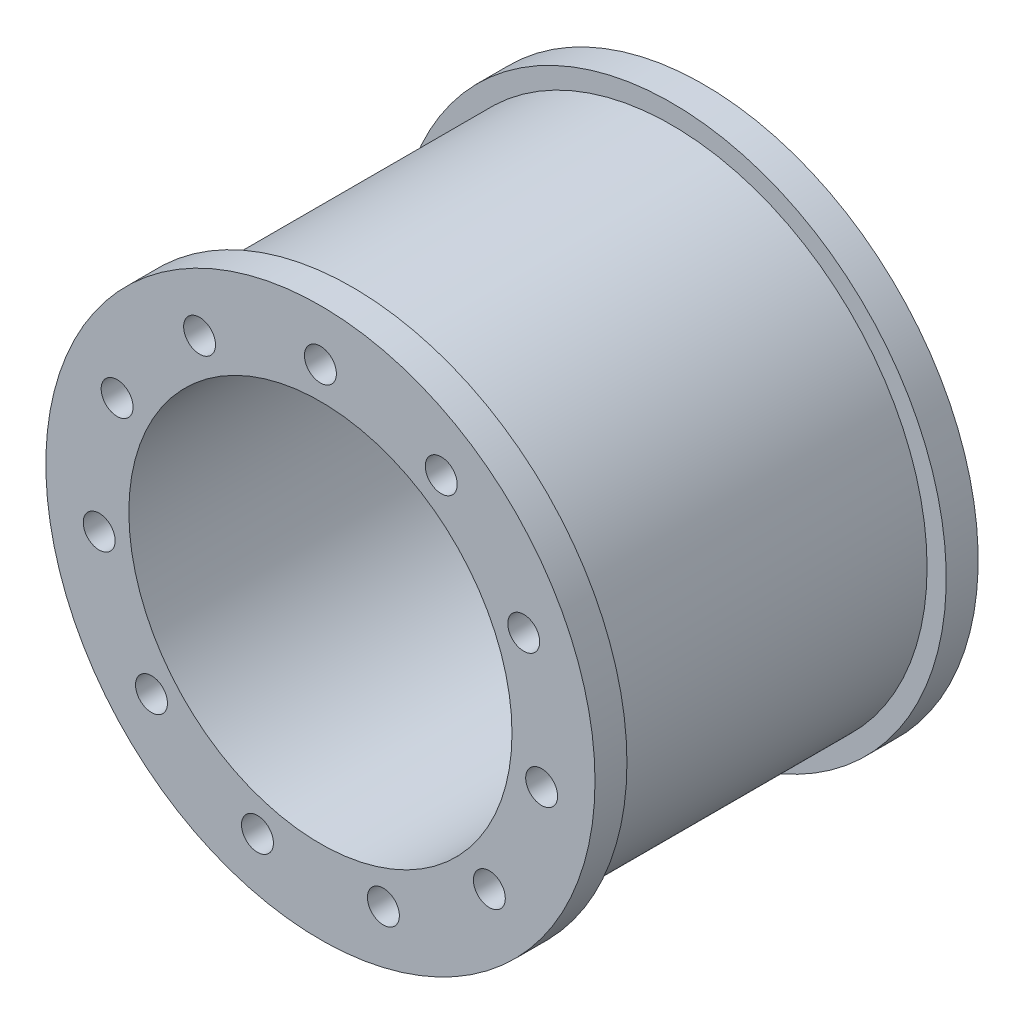
SolidWorks part; units mm, degrees
material "PET"
ref_plane "Front Plane" through (0, 0, 0) normal (0, 0, 1) x (1, 0, 0)
ref_plane "Top Plane" through (0, 0, 0) normal (0, 1, 0) x (1, 0, 0)
ref_plane "Right Plane" through (0, 0, 0) normal (1, 0, 0) x (0, 0, -1)
sketch "Sketch1" plane through (0, 0, 0) normal (0, 0, 1) x (1, 0, 0)
  circle A0 centre (0, 0) radius 40
  circle A1 centre (0, 0) radius 30
  circle A2 centre (0, 0) radius 35 construction
  circle A3 centre (0, 35) radius 2.5
  circle A4 centre (18.9224, 29.4439) radius 2.5
  circle A5 centre (31.8371, 14.5395) radius 2.5
  circle A6 centre (34.6438, -4.981) radius 2.5
  circle A7 centre (26.4512, -22.9201) radius 2.5
  circle A8 centre (9.8606, -33.5823) radius 2.5
  circle A9 centre (-9.8606, -33.5823) radius 2.5
  circle A10 centre (-26.4512, -22.9201) radius 2.5
  circle A11 centre (-34.6438, -4.981) radius 2.5
  circle A12 centre (-31.8371, 14.5395) radius 2.5
  circle A13 centre (-18.9224, 29.4439) radius 2.5
  point P29 (0, 0)
  dimension "D1" = 60
  dimension "D2" = 80
  dimension "D3" = 70
  dimension "D4" = 5
  dimension "D5" = 11
extrude "Boss-Extrude1" add sketch "Sketch1" along normal blind 50
sketch "Sketch2" plane through (0, 0, 0) normal (0, 0, -1) x (-1, 0, 0)
  circle A0 centre (0, 0) radius 43
  circle A1 centre (0, 0) radius 40 construction
  circle A2 centre (0, 0) radius 30
  circle A3 centre (0, 0) radius 30 construction
  dimension "D1" = 3
extrude "Boss-Extrude2" add sketch "Sketch2" along normal blind 5
sketch "Sketch3" plane through (0, 0, 50) normal (0, 0, 1) x (1, 0, 0)
  circle A0 centre (0, 0) radius 43
  circle A1 centre (0, 0) radius 30
  circle A2 centre (31.8371, 14.5395) radius 2.5 construction
  circle A3 centre (34.6438, -4.981) radius 2.5 construction
  circle A4 centre (26.4512, -22.9201) radius 2.5 construction
  circle A5 centre (9.8606, -33.5823) radius 2.5 construction
  circle A6 centre (-9.8606, -33.5823) radius 2.5 construction
  circle A7 centre (-26.4512, -22.9201) radius 2.5 construction
  circle A8 centre (-34.6438, -4.981) radius 2.5 construction
  circle A9 centre (-31.8371, 14.5395) radius 2.5 construction
  circle A10 centre (-18.9224, 29.4439) radius 2.5 construction
  circle A11 centre (0, 35) radius 2.5 construction
  circle A12 centre (18.9224, 29.4439) radius 2.5 construction
  circle A13 centre (31.8371, 14.5395) radius 2.5
  circle A14 centre (34.6438, -4.981) radius 2.5
  circle A15 centre (26.4512, -22.9201) radius 2.5
  circle A16 centre (9.8606, -33.5823) radius 2.5
  circle A17 centre (-9.8606, -33.5823) radius 2.5
  circle A18 centre (-26.4512, -22.9201) radius 2.5
  circle A19 centre (-34.6438, -4.981) radius 2.5
  circle A20 centre (-31.8371, 14.5395) radius 2.5
  circle A21 centre (-18.9224, 29.4439) radius 2.5
  circle A22 centre (0, 35) radius 2.5
  circle A23 centre (18.9224, 29.4439) radius 2.5
  circle A24 centre (0, 0) radius 30 construction
  circle A25 centre (0, 0) radius 43 construction
extrude "Boss-Extrude3" add sketch "Sketch3" along normal blind 5
